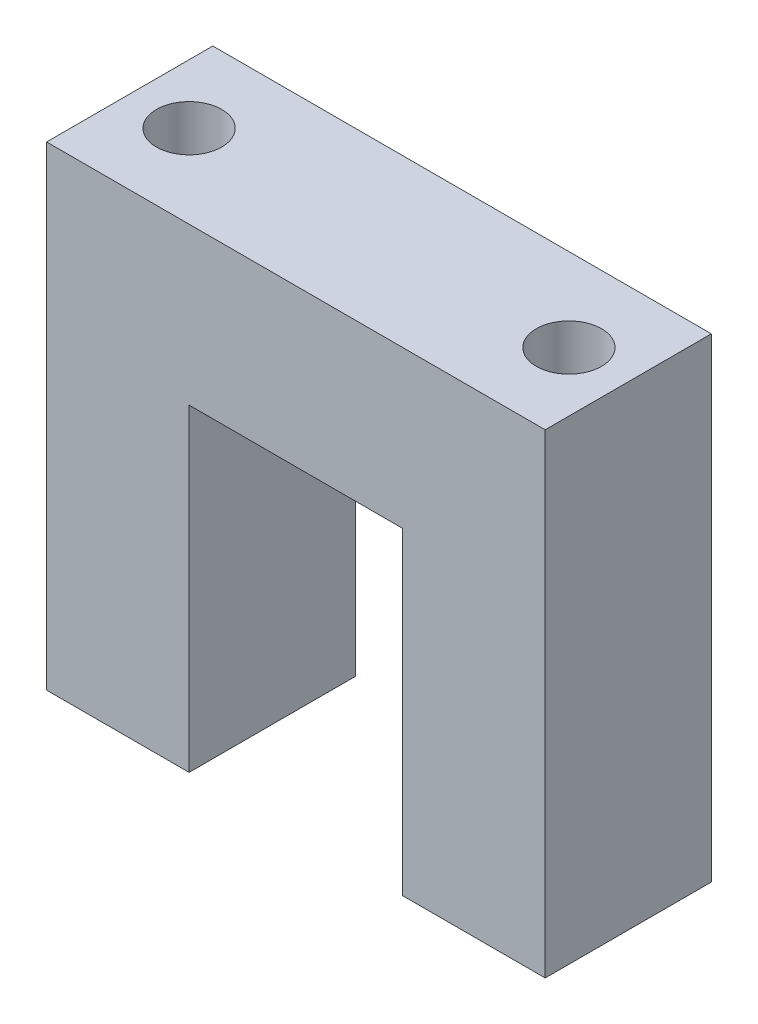
SolidWorks part; units mm, degrees
ref_plane "Front Plane" through (0, 0, 0) normal (0, 0, 1) x (1, 0, 0)
ref_plane "Top Plane" through (0, 0, 0) normal (0, 1, 0) x (1, 0, 0)
ref_plane "Right Plane" through (0, 0, 0) normal (1, 0, 0) x (0, 0, -1)
sketch "Sketch3" plane through (0, 0, 0) normal (0, 0, 1) x (1, 0, 0)
  line L0 (-9, 0) -> (-21, 0)
  line L1 (-21, 0) -> (-21, 40)
  line L2 (-21, 40) -> (21, 40)
  line L3 (21, 40) -> (21, 0)
  line L4 (21, 0) -> (9, 0)
  line L5 (9, 0) -> (9, 26.8)
  line L6 (9, 26.8) -> (-9, 26.8)
  line L7 (-9, 26.8) -> (-9, 0)
  point P4 (0, 26.8)
  point P9 (0, 40)
  dimension "D1" = 26.8
  dimension "D2" = 12
  dimension "D3" = 18
  dimension "D4" = 40
extrude "Boss-Extrude1" add sketch "Sketch3" along normal mid plane 14
sketch "Sketch4" plane through (0, 40, 0) normal (0, 1, 0) x (1, 0, 0)
  line L0 (-22, 0) -> (22, 0) construction
  line L1 (0, -10.6236) -> (0, 10.6236) construction
  circle A0 centre (-16, 0) radius 2.75
  circle A1 centre (16, 0) radius 2.75
  dimension "D1" = 5.5
  dimension "D2" = 32
  dimension "D3" = 16
extrude "Cut-Extrude1" cut sketch "Sketch4" against normal up to surface (40 mm away) up to face at (-15, 0, 0)
